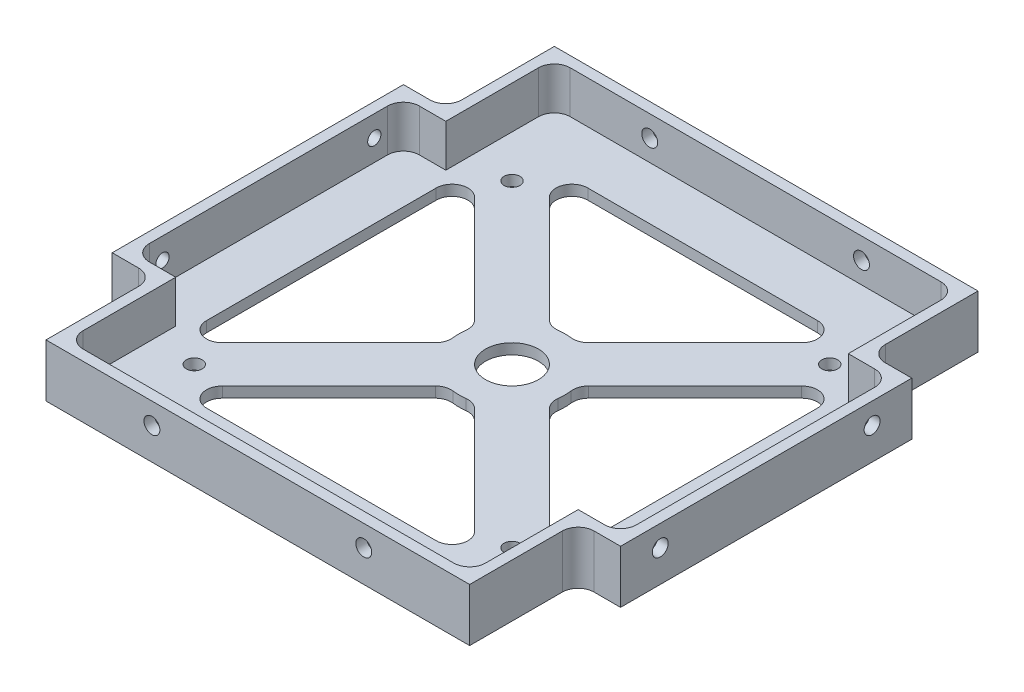
SolidWorks part; units mm, degrees
material "6061-T6 (SS)"
ref_plane "Front Plane" through (0, 0, 0) normal (0, 0, 1) x (1, 0, 0)
ref_plane "Top Plane" through (0, 0, 0) normal (0, 1, 0) x (1, 0, 0)
ref_plane "Right Plane" through (0, 0, 0) normal (1, 0, 0) x (0, 0, -1)
sketch "Sketch1" plane through (0, 0, 0) normal (0, 1, 0) x (1, 0, 0)
  line L0 (0, 8) -> (8, 0)
  line L1 (0, 0) -> (96, 0)
  line L2 (0, 0) -> (0, 96)
  line L3 (0, 96) -> (96, 96)
  line L4 (96, 0) -> (96, 96)
  line L5 (48, 96) -> (48, 0) construction
  line L6 (0, 48) -> (96, 48) construction
  line L7 (96, 8) -> (88, 0)
  line L8 (96, 88) -> (88, 96)
  line L9 (0, 88) -> (8, 96)
  dimension "D1" = 96
  dimension "D2" = 96
  dimension "D3" = 8
  dimension "D4" = 8
extrude "Boss-Extrude1" add sketch "Sketch1" along normal blind 10 contours L9 L2 L0 L1 L7 L4 L8 L3
sketch "Sketch2" plane through (0, 0, 0) normal (0, -1, 0) x (-1, 0, 0)
  line L0 (-4, 92) -> (-92, 4) construction
  line L1 (0, 88) -> (-8, 96) construction
  line L2 (-96, 8) -> (-88, 0) construction
  line L3 (-92, 92) -> (-4, 4) construction
  line L4 (-96, 88) -> (-88, 96) construction
  line L5 (0, 8) -> (-8, 0) construction
  line L6 (-12, 84) -> (-84, 84) construction
  line L7 (-84, 84) -> (-84, 12) construction
  line L8 (-84, 12) -> (-12, 12) construction
  line L9 (-12, 12) -> (-12, 84) construction
  line L10 (-8, 96) -> (-88, 96) construction
  line L12 (-19.0711, 84) -> (-84, 19.0711)
  line L13 (-12, 76.9289) -> (-76.9289, 12)
  line L14 (-12, 19.0711) -> (-76.9289, 84)
  line L15 (-19.0711, 12) -> (-84, 76.9289)
  line L16 (-12, 76.9289) -> (-12, 19.0711)
  line L17 (-19.0711, 12) -> (-76.9289, 12)
  line L18 (-84, 19.0711) -> (-84, 76.9289)
  line L19 (-76.9289, 84) -> (-19.0711, 84)
  circle A0 centre (-48, 48) radius 10
  circle A1 centre (-48, 48) radius 5
  dimension "D6" = 20
  dimension "D7" = 10
  dimension "D1" = 12
  dimension "D2" = 10
  dimension "D3" = 5
  dimension "D4" = 10
  dimension "D5" = 5
extrude "Cut-Extrude1" cut sketch "Sketch2" against normal through all contours A0 L12 L19 L14 | A0 L14 L16 L13 | A0 L13 L17 L15 | A0 L15 L18 L12 | A1
fillet "Fillet1" radius 3 16 edges at (19.0711, 5, -12) (76.9289, 5, -12) (50.5882, 5, -38.3407) (38.3407, 5, -50.5882) (45.4118, 5, -38.3407) (57.6593, 5, -50.5882) (12, 5, -19.0711) (38.3407, 5, -45.4118) (50.5882, 5, -57.6593) (84, 5, -19.0711) (84, 5, -76.9289) (57.6593, 5, -45.4118) (45.4118, 5, -57.6593) (76.9289, 5, -84) (19.0711, 5, -84) (12, 5, -76.9289)
sketch "Sketch5" plane through (0, 10, 0) normal (0, 1, 0) x (1, 0, 0)
  line L0 (8, 0) -> (8, 20.5)
  line L3 (0, 8) -> (8, 0)
  line L4 (0, 8) -> (0, 20.5)
  line L5 (0, 8) -> (0, 88) construction
  line L6 (0, 20.5) -> (8, 20.5)
  line L7 (0, 48) -> (96, 48) construction
  line L8 (96, 8) -> (96, 88) construction
  line L9 (48, 96) -> (48, 0) construction
  line L10 (8, 96) -> (88, 96) construction
  line L11 (8, 0) -> (88, 0) construction
  line L12 (96, 8) -> (88, 0)
  line L13 (96, 8) -> (96, 20.5)
  line L14 (96, 20.5) -> (88, 20.5)
  line L15 (88, 0) -> (88, 20.5)
  line L16 (96, 75.5) -> (88, 75.5)
  line L17 (96, 88) -> (96, 75.5)
  line L18 (96, 88) -> (88, 96)
  line L19 (88, 96) -> (88, 75.5)
  line L20 (8, 96) -> (8, 75.5)
  line L21 (0, 88) -> (8, 96)
  line L22 (0, 88) -> (0, 75.5)
  line L23 (0, 75.5) -> (8, 75.5)
  dimension "D1" = 20.5
extrude "Cut-Extrude4" cut sketch "Sketch5" against normal through all
sketch "Sketch6" plane through (0, 10, 0) normal (0, 1, 0) x (1, 0, 0)
  line L90 (86, 73.5) -> (86, 94)
  line L91 (94, 73.5) -> (86, 73.5)
  line L92 (94, 22.5) -> (94, 73.5)
  line L93 (86, 22.5) -> (94, 22.5)
  line L94 (86, 2) -> (86, 22.5)
  line L95 (10, 2) -> (86, 2)
  line L96 (10, 22.5) -> (10, 2)
  line L97 (2, 22.5) -> (10, 22.5)
  line L98 (2, 73.5) -> (2, 22.5)
  line L99 (10, 73.5) -> (2, 73.5)
  line L100 (10, 94) -> (10, 73.5)
  line L101 (86, 94) -> (10, 94)
  line L102 (86, 73.5) -> (86, 94)
  line L103 (94, 73.5) -> (86, 73.5)
  line L104 (94, 22.5) -> (94, 73.5)
  line L105 (86, 22.5) -> (94, 22.5)
  line L106 (86, 2) -> (86, 22.5)
  line L107 (10, 2) -> (86, 2)
  line L108 (10, 22.5) -> (10, 2)
  line L109 (2, 22.5) -> (10, 22.5)
  line L110 (2, 73.5) -> (2, 22.5)
  line L111 (10, 73.5) -> (2, 73.5)
  line L112 (10, 94) -> (10, 73.5)
  line L113 (86, 94) -> (10, 94)
  dimension "D1" = 2
extrude "Cut-Extrude5" cut sketch "Sketch6" against normal blind 8
fillet "Fillet2" radius 3 12 edges at (88, 5, -75.5) (88, 5, -20.5) (8, 5, -75.5) (8, 5, -20.5) (86, 6, -94) (94, 6, -73.5) (94, 6, -22.5) (86, 6, -2) (10, 6, -94) (10, 6, -2) (2, 6, -22.5) (2, 6, -73.5)
sketch "Sketch7" plane through (0, 0, 0) normal (0, -1, 0) x (1, 0, 0)
  line L0 (78, -18) -> (18, -18) construction
  line L1 (78, -78) -> (18, -78)
  line L2 (78, -78) -> (78, -18)
  line L3 (78, -18) -> (18, -18)
  line L4 (18, -78) -> (18, -18)
  line L5 (78, -78) -> (18, -18) construction
  line L6 (78, -18) -> (18, -78) construction
  line L7 (78, -18) -> (78, -78) construction
  line L8 (8, 0) -> (88, 0) construction
  line L9 (96, -20.5) -> (96, -75.5) construction
  line L10 (88, -96) -> (88, -78.5) construction
  circle A0 centre (78, -18) radius 1.5
  circle A1 centre (18, -18) radius 1.5
  circle A2 centre (18, -78) radius 1.5
  circle A3 centre (78, -78) radius 1.5
  point P0 (48, -48)
  dimension "D1" = 2
  dimension "D5" = 3
  dimension "D8" = 10
  dimension "D2" = 60
  dimension "D3" = 60
  dimension "D6" = 18
  dimension "D7" = 18
  dimension "D4" = 2
sketch "Sketch8" plane through (0, 0, 0) normal (0, 0, 1) x (1, 0, 0)
  line L0 (8, 6) -> (88, 6) construction
  line L1 (8, 10) -> (8, 0) construction
  line L2 (88, 10) -> (88, 0) construction
  line L3 (8, 0) -> (88, 0) construction
  line L4 (48, 10) -> (48, 0) construction
  line L5 (8, 10) -> (88, 10) construction
  dimension "D1" = 6
sketch "Sketch9" plane through (0, 0, 0) normal (-1, 0, 0) x (0, 0, 1)
  line L0 (-75.5, 6) -> (-20.5, 6) construction
  line L1 (-75.5, 0) -> (-75.5, 10) construction
  line L2 (-20.5, 0) -> (-20.5, 10) construction
  line L3 (-20.5, 0) -> (-75.5, 0) construction
  line L4 (-48, 10) -> (-48, 0) construction
  line L5 (-20.5, 10) -> (-75.5, 10) construction
  dimension "D1" = 6
hole_wizard "Ø3.0mm Dowel Hole1" positions "Sketch12" profile "Sketch13" hole size "Ø3.0" standard "ANSI Metric"
sketch "Sketch12" plane through (0, 0, 0) normal (0, 0, 1) x (1, 0, 0)
  line L0 (8, 6) -> (88, 6) construction
  line L2 (48, 10) -> (48, 0) construction
  point P0 (28, 6)
  point P4 (68, 6)
  dimension "D1" = 40
  dimension "D2" = 20
sketch "Sketch13" plane through (28, 6, 0) normal (1, 0, 0) x (0, -1, 0)
  line L0 (0, 0) -> (0, 8.4013)
  line L1 (0, 8.4013) -> (1.5, 7.5)
  line L2 (1.5, 7.5) -> (1.5, 0)
  line L5 (1.5, 0) -> (0, 0)
  line L10 (0, 8.4013) -> (-1.5, 7.5) construction
  line L11 (0, -6.35) -> (0, 107.95) construction
  dimension "Hole Dia." = 3
  dimension "Hole Depth" = 7.5
  dimension "Drill Angle" = 118
hole_wizard "Tap Drill for M3x0.5 Tap1" positions "Sketch14" profile "Sketch15" hole size "M3x0.5" standard "ANSI Metric" end condition up to next
sketch "Sketch14" plane through (0, 0, 0) normal (-1, 0, 0) x (0, 0, 1)
  line L0 (-75.5, 6) -> (-20.5, 6) construction
  line L1 (-48, 10) -> (-48, 0) construction
  point P0 (-68, 6)
  point P4 (-28, 6)
  dimension "D1" = 40
  dimension "D2" = 20
sketch "Sketch15" plane through (0, 6, -68) normal (0, 1, 0) x (0, 0, 1)
  line L0 (0, 0) -> (0, 2)
  line L1 (0, 2) -> (1.25, 2)
  line L2 (1.25, 2) -> (1.25, 0)
  line L5 (1.25, 0) -> (0, 0)
  line L11 (0, -6.35) -> (0, 107.95) construction
  dimension "Thru Hole Dia." = 2.5
  dimension "Thru Hole Depth" = 2
ref_plane "Plane1" through (48, 0, 0) normal (-1, 0, 0) x (0, 0, 1)
ref_plane "Plane2" through (0, 0, -48) normal (0, 0, 1) x (1, 0, 0)
mirror "Mirror1" about plane through (0, 0, -48) normal (0, 0, 1) of "Ø3.0mm Dowel Hole1"
sketch "Sketch16" plane through (0, 0, 0) normal (-1, 0, 0) x (0, 0, 1)
  line L0 (-48, 0) -> (-48, 10) construction
  line L1 (-20.5, 0) -> (-75.5, 0) construction
  line L2 (-20.5, 10) -> (-75.5, 10) construction
  line L4 (-40.9661, 4.5188) -> (-54.475, 4.5188) construction
  point P6 (-40.9661, 4.5188)
hole_wizard "Ø3.0mm Dowel Hole3" positions "3DSketch1" profile "Sketch17" hole size "Ø3.0" standard "ANSI Metric" end condition through all
sketch3d "3DSketch1"
  point P0 (78, 0, -18)
  point P3 (78, 0, -78)
  point P6 (18, 0, -78)
  point P9 (18, 0, -18)
sketch "Sketch17" plane through (78, 0, -18) normal (1, 0, 0) x (0, 0, -1)
  line L0 (0, 0) -> (0, 10)
  line L1 (0, 10) -> (1.5, 10)
  line L2 (1.5, 10) -> (1.5, 0)
  line L5 (1.5, 0) -> (0, 0)
  line L11 (0, -6.35) -> (0, 107.95) construction
  dimension "Thru Hole Dia." = 3
  dimension "Thru Hole Depth" = 10
sketch "Sketch18" plane through (96, 0, 0) normal (1, 0, 0) x (0, 0, -1)
  line L1 (20.5, 0) -> (75.5, 0) construction
  line L4 (75.5, 0) -> (75.5, 10) construction
  point P8 (28, 6)
  point P9 (68, 6)
  dimension "D1" = 7.5
  dimension "D2" = 6
  dimension "D3" = 40
  dimension "D4" = 6
hole_wizard "Ø3.0mm Dowel Hole4" positions "3DSketch2" profile "Sketch19" hole size "Ø3.0" standard "ANSI Metric" end condition up to next
sketch3d "3DSketch2"
  point P0 (96, 6, -68)
  point P3 (96, 6, -28)
sketch "Sketch19" plane through (96, 6, -68) normal (0, 1, 0) x (0, 0, -1)
  line L0 (0, 0) -> (0, 2)
  line L1 (0, 2) -> (1.5, 2)
  line L2 (1.5, 2) -> (1.5, 0)
  line L5 (1.5, 0) -> (0, 0)
  line L11 (0, -6.35) -> (0, 107.95) construction
  dimension "Thru Hole Dia." = 3
  dimension "Thru Hole Depth" = 2
